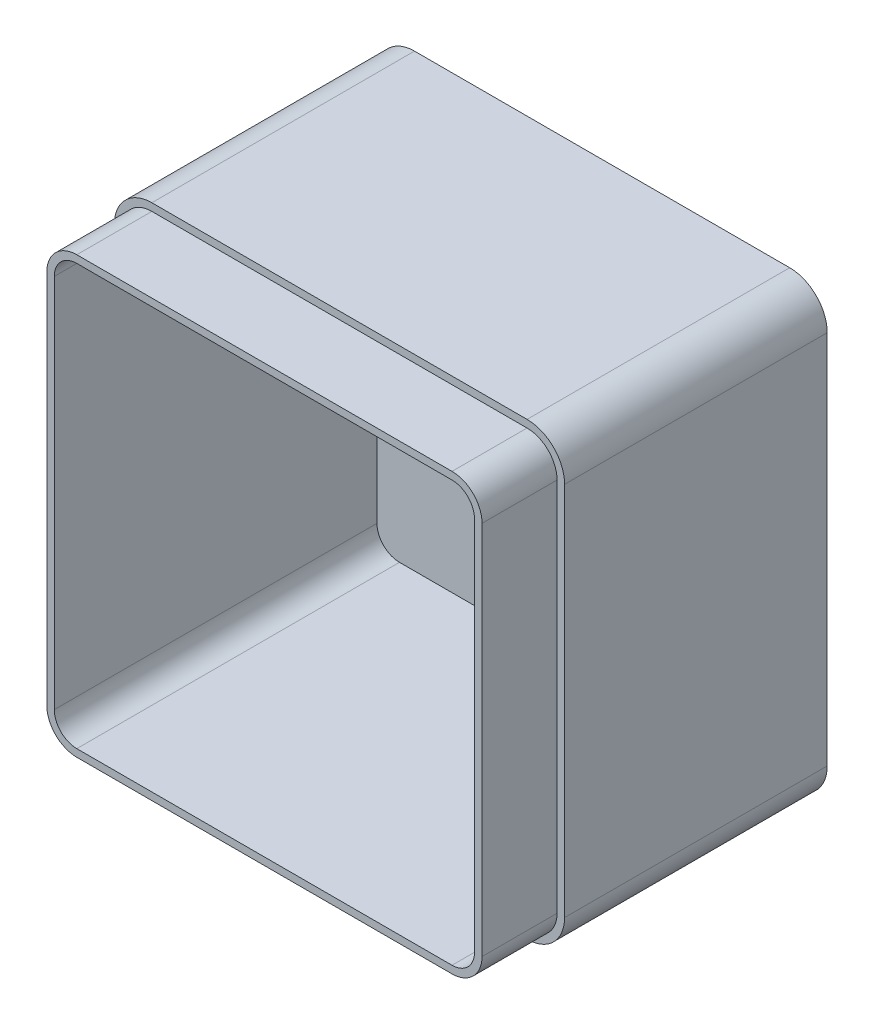
SolidWorks part; units mm, degrees
ref_plane "Front Plane" through (0, 0, 0) normal (0, 0, 1) x (1, 0, 0)
ref_plane "Top Plane" through (0, 0, 0) normal (0, 1, 0) x (1, 0, 0)
ref_plane "Right Plane" through (0, 0, 0) normal (1, 0, 0) x (0, 0, -1)
sketch "Sketch2" plane through (0, 0, 0) normal (0, 0, 1) x (1, 0, 0)
  line L1 (0, 0) -> (120, 0)
  line L2 (0, 0) -> (0, 120)
  line L3 (0, 120) -> (120, 120)
  line L4 (120, 0) -> (120, 120)
  dimension "D1" = 120
  dimension "D2" = 120
extrude "Boss-Extrude1" add sketch "Sketch2" along normal blind 90
fillet "Fillet1" radius 10 4 edges at (0, 0, 45) (120, 0, 45) (0, 120, 45) (120, 120, 45)
shell "Shell1" thickness 4
sketch "Sketch9" plane through (0, 0, 90) normal (0, 0, 1) x (1, 0, 0)
  line L0 (110, 120) -> (10, 120) construction
  line L1 (120, 10) -> (120, 110) construction
  line L2 (10, 0) -> (110, 0) construction
  line L3 (0, 110) -> (0, 10) construction
  line L4 (110, 120) -> (10, 120)
  line L5 (120, 10) -> (120, 110)
  line L6 (10, 0) -> (110, 0)
  line L7 (0, 110) -> (0, 10)
  arc A0 (10, 120) -> (0, 110) centre (10, 110) ccw construction
  arc A1 (120, 110) -> (110, 120) centre (110, 110) ccw construction
  arc A2 (110, 0) -> (120, 10) centre (110, 10) ccw construction
  arc A3 (0, 10) -> (10, 0) centre (10, 10) ccw construction
  arc A4 (10, 120) -> (0, 110) centre (10, 110) ccw
  arc A5 (120, 110) -> (110, 120) centre (110, 110) ccw
  arc A6 (110, 0) -> (120, 10) centre (110, 10) ccw
  arc A7 (0, 10) -> (10, 0) centre (10, 10) ccw
sketch "Sketch10" plane through (0, 0, 90) normal (0, 0, 1) x (1, 0, 0)
  line L0 (2, 110) -> (2, 10)
  line L1 (10, 2) -> (110, 2)
  line L2 (118, 10) -> (118, 110)
  line L3 (110, 118) -> (10, 118)
  line L4 (0, 110) -> (0, 10)
  line L5 (10, 0) -> (110, 0)
  line L6 (120, 10) -> (120, 110)
  line L7 (110, 120) -> (10, 120)
  line L8 (0, 110) -> (0, 10)
  line L9 (10, 0) -> (110, 0)
  line L10 (120, 10) -> (120, 110)
  line L11 (110, 120) -> (10, 120)
  arc A0 (2, 10) -> (10, 2) centre (10, 10) ccw
  arc A1 (110, 2) -> (118, 10) centre (110, 10) ccw
  arc A2 (118, 110) -> (110, 118) centre (110, 110) ccw
  arc A3 (10, 118) -> (2, 110) centre (10, 110) ccw
  arc A4 (0, 10) -> (10, 0) centre (10, 10) ccw
  arc A5 (110, 0) -> (120, 10) centre (110, 10) ccw
  arc A6 (120, 110) -> (110, 120) centre (110, 110) ccw
  arc A7 (10, 120) -> (0, 110) centre (10, 110) ccw
  arc A8 (0, 10) -> (10, 0) centre (10, 10) ccw
  arc A9 (110, 0) -> (120, 10) centre (110, 10) ccw
  arc A10 (120, 110) -> (110, 120) centre (110, 110) ccw
  arc A11 (10, 120) -> (0, 110) centre (10, 110) ccw
  dimension "D1" = 0
  dimension "D2" = 2
extrude "Cut-Extrude7" cut sketch "Sketch10" against normal blind 20
